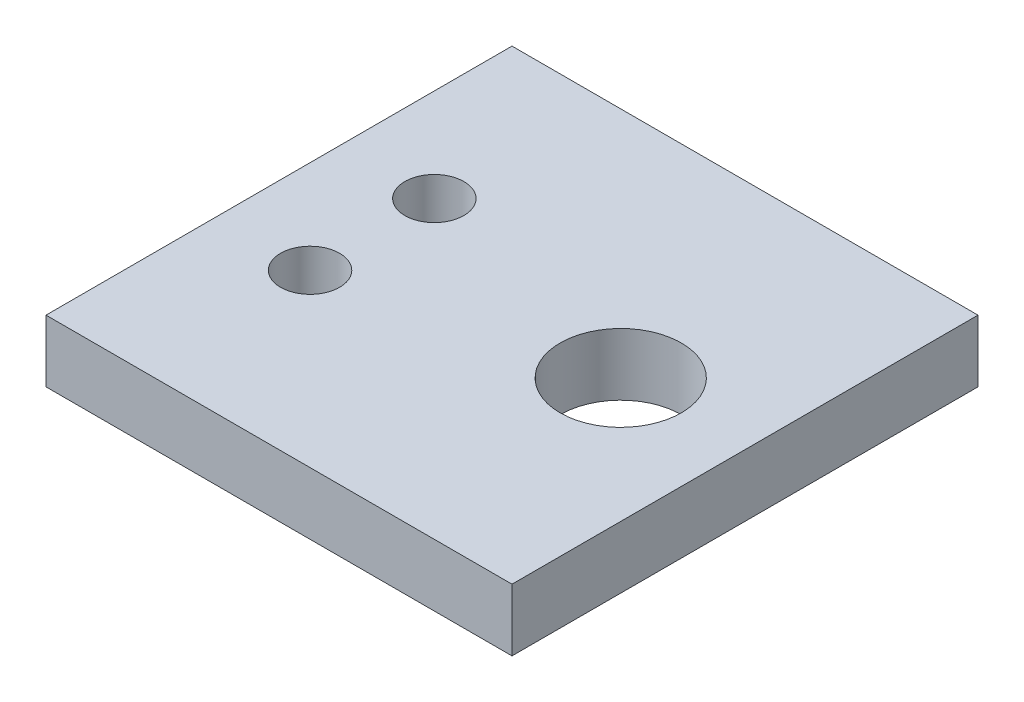
SolidWorks part; units mm, degrees
ref_plane "Front Plane" through (0, 0, 0) normal (0, 0, 1) x (1, 0, 0)
ref_plane "Top Plane" through (0, 0, 0) normal (0, 1, 0) x (1, 0, 0)
ref_plane "Right Plane" through (0, 0, 0) normal (1, 0, 0) x (0, 0, -1)
sketch "Sketch2" plane through (0, 0, 0) normal (0, 1, 0) x (1, 0, 0)
  line L1 (-7.5, 7.5) -> (7.5, 7.5)
  line L2 (-7.5, 7.5) -> (-7.5, -7.5)
  line L3 (-7.5, -7.5) -> (7.5, -7.5)
  line L4 (7.5, 7.5) -> (7.5, -7.5)
  line L5 (-7.5, 7.5) -> (7.5, -7.5) construction
  line L6 (-7.5, -7.5) -> (7.5, 7.5) construction
  point P0 (0, 0)
  dimension "D1" = 15
  dimension "D2" = 15
extrude "Boss-Extrude1" add sketch "Sketch2" along normal blind 2
sketch "Sketch3" plane through (0, 2, 0) normal (0, 1, 0) x (1, 0, 0)
  line L0 (-7.5, 7.5) -> (-7.5, -7.5) construction
  line L2 (-4.5, 2) -> (-4.5, -2) construction
  line L3 (-7.5, -7.5) -> (7.5, -7.5) construction
  circle A0 centre (-4.5, -2) radius 0.95
  circle A1 centre (-4.5, 2) radius 0.95
  point P6 (-4.5, 0)
  dimension "D1" = 4
  dimension "D2" = 3
  dimension "D3" = 7.5
extrude "Cut-Extrude1" cut sketch "Sketch3" against normal blind 2
sketch "Sketch4" plane through (0, 2, 0) normal (0, 1, 0) x (1, 0, 0)
  line L0 (7.5, -7.5) -> (7.5, 7.5) construction
  circle A0 centre (3.5, 0) radius 1.95
  dimension "D1" = 4
extrude "Cut-Extrude2" cut sketch "Sketch4" against normal blind 2
